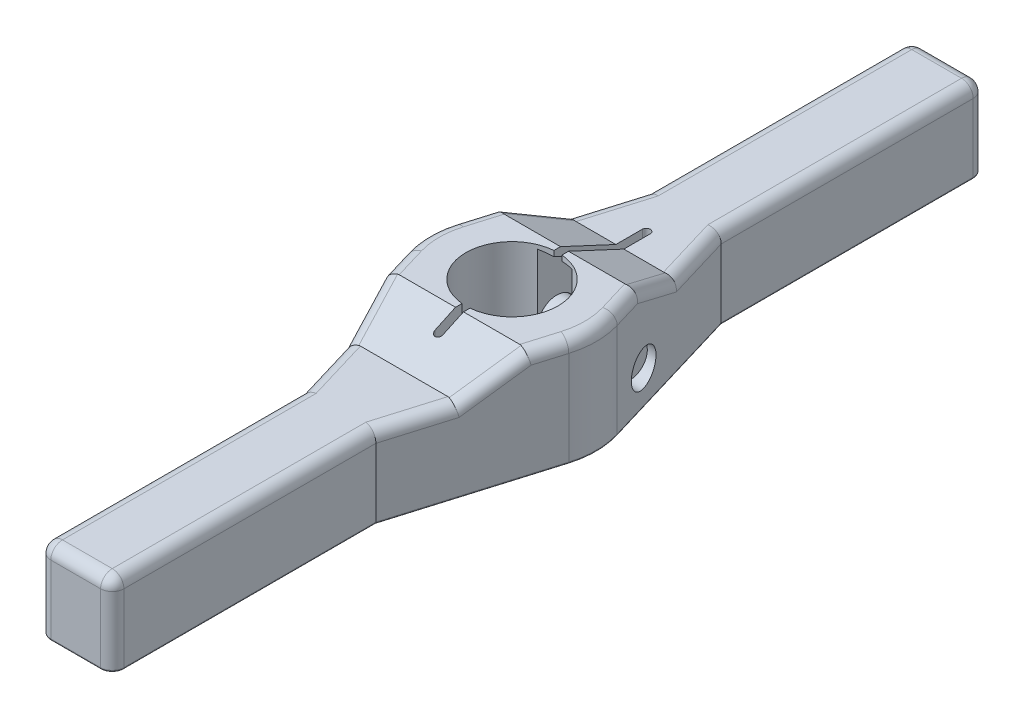
SolidWorks part; units mm, degrees
material "Alloy Steel"
ref_plane "Front Plane" through (0, 0, 0) normal (0, 0, 1) x (1, 0, 0)
ref_plane "Top Plane" through (0, 0, 0) normal (0, 1, 0) x (1, 0, 0)
ref_plane "Right Plane" through (0, 0, 0) normal (1, 0, 0) x (0, 0, -1)
sketch "Sketch1" plane through (0, 0, 0) normal (0, 1, 0) x (1, 0, 0)
  line L0 (-15.113, 71.374) -> (-33.4614, 10.0044)
  line L1 (0, 63.5) -> (0, 0) construction
  line L2 (15.113, 71.374) -> (33.4614, 10.0044)
  line L3 (-15.113, 71.374) -> (15.113, 71.374)
  line L4 (0, 0) -> (74.928, 0) construction
  line L5 (-15.113, -71.374) -> (-33.4614, -10.0044)
  line L6 (15.113, -71.374) -> (33.4614, -10.0044)
  line L7 (-15.113, -71.374) -> (15.113, -71.374)
  circle A0 centre (0, 0) radius 19.0691
  arc A1 (-33.4614, 10.0044) -> (-33.4614, -10.0044) centre (0, 0) ccw
  arc A2 (33.4614, -10.0044) -> (33.4614, 10.0044) centre (0, 0) ccw
  dimension "D1" = 38.1381
  dimension "D2" = 34.925
  dimension "D3" = 71.374
  dimension "D4" = 30.226
extrude "Extrude1" add sketch "Sketch1" along normal blind 44.45
sketch "Sketch2" plane through (0, 0, 0) normal (1, 0, 0) x (0, 0, -1)
  line L0 (21.6994, 44.45) -> (44.577, 33.782)
  line L1 (71.374, 44.45) -> (10.0044, 44.45) construction
  line L2 (44.577, 33.782) -> (71.374, 21.2864)
  line L4 (71.374, 44.45) -> (21.6994, 44.45)
  line L5 (71.374, 21.2864) -> (71.374, 44.45)
  line L7 (71.374, 0) -> (10.0044, 0) construction
  line L8 (71.374, 44.45) -> (71.374, 0) construction
  dimension "D1" = 33.782
  dimension "D2" = 25
  dimension "D3" = 44.577
extrude "Cut-Extrude1" cut sketch "Sketch2" against normal through all and the other way through all
sketch "Sketch3" plane through (0, 0, 0) normal (0, -1, 0) x (1, 0, 0)
  line L0 (0, 0) -> (0, -101.5721) construction
  line L1 (-7.1374, -10.3124) -> (-7.1374, -50.0126)
  line L2 (7.1374, -10.3124) -> (7.1374, -50.0126)
  arc A0 (-7.1374, -10.3124) -> (7.1374, -10.3124) centre (0, -10.3124) cw
  arc A1 (-7.1374, -50.0126) -> (7.1374, -50.0126) centre (0, -50.0126) ccw
  dimension "D1" = 3.175
  dimension "D2" = 57.15
  dimension "D3" = 14.2748
extrude "Cut-Extrude2" cut sketch "Sketch3" against normal offset from surface (46.2566 mm away) 3.175
sketch "Sketch4" plane through (0, 0, 0) normal (0, -1, 0) x (1, 0, 0)
  line L0 (0, 0) -> (0, -69.4753) construction
  line L1 (-1.651, 0) -> (-1.651, -55.499)
  line L2 (1.651, 0) -> (1.651, -55.499)
  line L3 (-1.651, 0) -> (1.651, 0)
  arc A0 (-1.651, -55.499) -> (1.651, -55.499) centre (0, -55.499) ccw
  arc A1 (-7.1374, -50.0126) -> (7.1374, -50.0126) centre (0, -50.0126) ccw construction
  dimension "D1" = 3.302
extrude "Cut-Extrude3" cut sketch "Sketch4" against normal through all
ref_plane "Plane1" through (0, 0, -25.629) normal (0, 0, 1) x (1, 0, 0)
sketch "Sketch11" plane through (0, 0, 0) normal (0, -1, 0) x (1, 0, 0)
  line L1 (-15.113, -71.374) -> (15.113, -71.374)
  line L2 (-15.113, -71.374) -> (-15.113, -180.34)
  line L3 (-15.113, -180.34) -> (15.113, -180.34)
  line L4 (15.113, -71.374) -> (15.113, -180.34)
  dimension "D1" = 180.34
extrude "Extrude4" add sketch "Sketch11" against normal blind 33.782
sketch "Sketch14" plane through (0, 0, -71.374) normal (0, 0, 1) x (1, 0, 0)
  line L0 (15.113, 33.782) -> (-15.113, 33.782) construction
  line L1 (15.113, 33.782) -> (-15.113, 33.782)
curve "Curve1"
sketch "Sketch12" plane through (0, 33.782, 0) normal (0, 1, 0) x (1, 0, 0)
  line L2 (1.651, 55.499) -> (1.651, 21.6994) construction
  line L3 (-1.651, 21.6994) -> (-1.651, 55.499) construction
  line L4 (15.113, 71.374) -> (29.9648, 21.6994) construction
  line L5 (-15.113, 71.374) -> (15.113, 71.374) construction
  line L6 (-29.9648, 21.6994) -> (-15.113, 71.374) construction
  line L7 (-1.651, 44.577) -> (-23.1248, 44.577)
  line L9 (1.651, 55.499) -> (1.651, 44.577)
  line L10 (-1.651, 44.577) -> (-1.651, 55.499)
  line L11 (15.113, 71.374) -> (23.1248, 44.577)
  line L12 (-15.113, 71.374) -> (15.113, 71.374)
  line L13 (-23.1248, 44.577) -> (-15.113, 71.374)
  line L15 (15.113, 44.577) -> (1.651, 44.577)
  line L16 (23.1248, 44.577) -> (1.651, 44.577)
  arc A0 (1.651, 55.499) -> (-1.651, 55.499) centre (0, 55.499) ccw construction
  arc A1 (1.651, 55.499) -> (-1.651, 55.499) centre (0, 55.499) ccw
  dimension "D1" = 0
extrude "Extrude5" add sketch "Sketch12" against normal up to surface (5.093 mm away)
sketch "Sketch5" plane through (0, 0, -25.629) normal (0, 0, 1) x (1, 0, 0)
  line L0 (-30.1073, 14.2748) -> (29.8831, 14.2748) construction
  line L1 (-34.925, 31.7373) -> (-25.3492, 31.7373)
  line L2 (-25.3492, 31.7373) -> (-25.3492, 22.4028)
  line L3 (-25.3492, 22.4028) -> (7.1374, 22.4028)
  line L4 (7.1374, 22.4028) -> (7.1374, 21.5392)
  line L5 (33.4614, 14.2748) -> (-34.925, 14.2748)
  line L6 (-34.925, 14.2748) -> (-34.925, 31.7373)
  line L7 (-34.925, 0) -> (-33.4614, 0) construction
  line L8 (-34.925, 44.45) -> (-34.925, 0) construction
  line L9 (7.1374, 0) -> (7.1374, 42.8197) construction
  line L10 (7.1374, 21.5392) -> (33.4614, 21.5392)
  line L11 (33.4614, 21.5392) -> (33.4614, 14.2748)
  line L14 (33.4614, 44.45) -> (33.4614, 0) construction
  dimension "D1" = 14.2748
  dimension "D2" = 16.256
  dimension "D3" = 34.925
  dimension "D4" = 9.5758
  dimension "D5" = 14.5288
revolve "Cut-Revolve1" cut sketch "Sketch5" angle 360 about L0
sketch "Sketch6" plane through (-25.3492, 0, 0) normal (-1, 0, 0) x (0, 0, 1)
  line L1 (-11.7709, 14.2748) -> (-18.6999, 26.2763)
  line L2 (-18.6999, 26.2763) -> (-32.5581, 26.2763)
  line L3 (-32.5581, 26.2763) -> (-39.4871, 14.2748)
  line L4 (-39.4871, 14.2748) -> (-32.5581, 2.2733)
  line L5 (-32.5581, 2.2733) -> (-18.6999, 2.2733)
  line L6 (-18.6999, 2.2733) -> (-11.7709, 14.2748)
  circle A0 centre (-25.629, 14.2748) radius 12.0015 construction
  dimension "D1" = 24.003
extrude "Extrude2" add sketch "Sketch6" along normal blind 10.0076
sketch "Sketch7" plane through (-25.3492, 0, 0) normal (-1, 0, 0) x (0, 0, 1)
  circle A0 centre (-25.629, 14.2748) radius 8.001
  dimension "D1" = 16.002
extrude "Extrude3" add sketch "Sketch7" against normal blind 48.387
sketch "Sketch8" plane through (0, 0, -25.629) normal (0, 0, 1) x (1, 0, 0)
  line L0 (-5.5513, 14.2748) -> (-39.7173, 14.2748) construction
  line L1 (7.1374, 14.2748) -> (-25.3492, 14.2748) construction
  line L2 (-25.1869, 14.2748) -> (-26.324, 14.2748) construction
  line L3 (-35.3568, 2.2733) -> (-35.3568, -0.9017)
  line L4 (-35.3568, -0.9017) -> (-33.5237, -0.9017)
  line L5 (-33.5237, -0.9017) -> (-35.3568, 2.2733)
  dimension "D1" = 30
  dimension "D2" = 3.175
revolve "Cut-Revolve2" cut sketch "Sketch8" angle 360 about L0
mirror "Mirror1" about plane through (0, 0, 0) normal (0, 0, 1) of "Cut-Extrude1"
mirror "Mirror2" about plane through (0, 0, 0) normal (0, 0, 1) of "Extrude4"
sketch "Sketch16" plane through (0, 33.782, 0) normal (0, 1, 0) x (1, 0, 0)
  line L0 (15.113, -71.374) -> (29.9648, -21.6994) construction
  line L1 (15.113, -71.374) -> (-15.113, -71.374) construction
  line L2 (-29.9648, -21.6994) -> (-15.113, -71.374) construction
  line L3 (15.113, -71.374) -> (23.1248, -44.577)
  line L4 (15.113, -71.374) -> (-15.113, -71.374)
  line L5 (-23.1248, -44.577) -> (-15.113, -71.374)
  line L6 (0, 0) -> (85.0401, 0) construction
  line L8 (-23.1248, -44.577) -> (23.1248, -44.577)
  line L9 (1.651, 44.577) -> (23.1248, 44.577) construction
extrude "Extrude6" add sketch "Sketch16" against normal up to surface (12.4956 mm away)
fillet "Fillet2" radius 4.826 4 edges at (-15.113, 16.891, 180.34) (15.113, 16.891, 180.34) (-15.113, 16.891, -180.34) (15.113, 16.891, -180.34)
fillet "Fillet1" radius 4.826 28 edges at (34.925, 44.45, 0) (19.1189, 33.782, -57.9755) (-19.1189, 33.782, -57.9755) (31.7131, 44.45, -15.8519) (31.7131, 44.45, 15.8519) (-34.925, 44.45, 0) (-15.113, 33.782, 123.444) (19.1189, 33.782, 57.9755) (-19.1189, 33.782, 57.9755) (-31.7131, 44.45, 15.8519) (15.113, 33.782, 123.444) (0, 33.782, 180.34) (-13.6995, 33.782, 178.9265) (13.6995, 33.782, 178.9265) (-31.7131, 44.45, -15.8519) (0, 33.782, -180.34) (15.113, 33.782, -123.444) (-13.6995, 33.782, -178.9265) (13.6995, 33.782, -178.9265) (-15.113, 33.782, -123.444)
fillet "Fillet3" radius 0.762 19 edges at (-32.6293, 0, -12.7876) (-25.566, 0, -35.6873) (-32.7495, 2.8928, -12.3855) (-15.113, 0, 123.444) (15.113, 0, 123.444) (0, 0, -180.34) (15.113, 0, -123.444) (0, 0, 180.34) (-13.6995, 0, -178.9265) (13.6995, 0, -178.9265) (-13.6995, 0, 178.9265) (13.6995, 0, 178.9265) (-24.2872, 0, 40.6892) (-34.925, 0, 0) (-20.4479, 0, -53.5306) (24.2872, 0, -40.6892) (34.925, 0, 0) (-15.113, 0, -123.444) (24.2872, 0, 40.6892)
sketch "Sketch17" plane through (0, 44.45, 0) normal (0, 1, 0) x (1, 0, 0)
  line L0 (-1.651, 0) -> (-1.651, -30.099)
  line L1 (1.651, 0) -> (1.651, -30.099)
  line L2 (-1.651, 21.6994) -> (-1.651, 44.577) construction
  line L3 (1.651, 44.577) -> (1.651, 21.6994) construction
  line L4 (-1.651, 0) -> (1.651, 0)
  arc A0 (-1.651, -30.099) -> (1.651, -30.099) centre (0, -30.099) ccw
  dimension "D1" = 30.099
extrude "Cut-Extrude4" cut sketch "Sketch17" against normal through all
